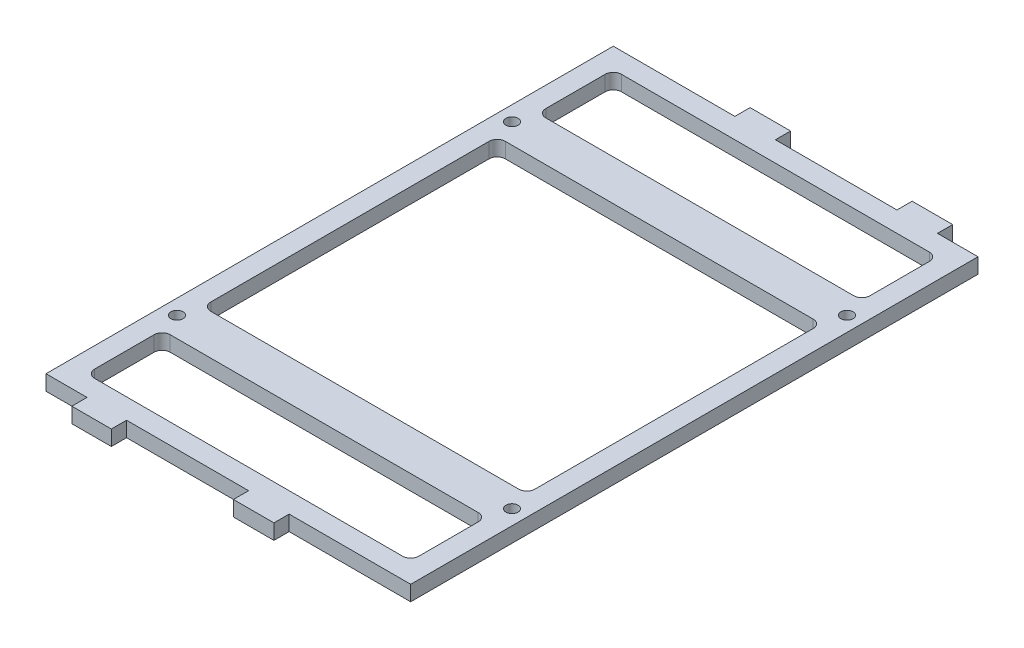
SolidWorks part; units mm, degrees
material "6061-T6 (SS)"
ref_plane "Front Plane" through (0, 0, 0) normal (0, 0, 1) x (1, 0, 0)
ref_plane "Top Plane" through (0, 0, 0) normal (0, 1, 0) x (1, 0, 0)
ref_plane "Right Plane" through (0, 0, 0) normal (1, 0, 0) x (0, 0, -1)
sketch "Sketch1" plane through (0, 0, 0) normal (0, 1, 0) x (1, 0, 0)
  line L0 (50.8, 82.55) -> (-50.8, 82.55)
  line L1 (57.15, 88.9) -> (-57.15, 88.9)
  line L2 (57.15, 88.9) -> (57.15, -88.9)
  line L3 (57.15, -88.9) -> (-57.15, -88.9)
  line L4 (-57.15, 88.9) -> (-57.15, -88.9)
  line L5 (57.15, 88.9) -> (-57.15, -88.9) construction
  line L6 (57.15, -88.9) -> (-57.15, 88.9) construction
  line L7 (-50.8, 82.55) -> (-50.8, -82.55)
  line L8 (50.8, -82.55) -> (-50.8, -82.55)
  line L9 (50.8, 82.55) -> (50.8, -82.55)
  point P0 (0, 0)
  dimension "D1" = 114.3
  dimension "D2" = 177.8
  dimension "D3" = 6.35
extrude "Boss-Extrude1" add sketch "Sketch1" along normal blind 4.7625
sketch "Sketch2" plane through (0, 0, 88.9) normal (0, 0, 1) x (1, 0, 0)
  line L0 (-57.15, 2.3813) -> (57.15, 2.3813) construction
  line L1 (-57.15, 4.7625) -> (-57.15, 0) construction
  line L2 (57.15, 4.7625) -> (57.15, 0) construction
  line L3 (-57.15, 0) -> (57.15, 0) construction
  line L4 (-31.9066, 4.7625) -> (-44.2934, 4.7625)
  line L5 (-31.9066, 4.7625) -> (-31.9066, 0)
  line L6 (-31.9066, 0) -> (-44.2934, 0)
  line L7 (-44.2934, 4.7625) -> (-44.2934, 0)
  line L8 (-31.9066, 4.7625) -> (-44.2934, 0) construction
  line L9 (-31.9066, 0) -> (-44.2934, 4.7625) construction
  line L11 (19.05, 4.7625) -> (6.35, 4.7625)
  line L12 (19.05, 4.7625) -> (19.05, 0)
  line L13 (19.05, 0) -> (6.35, 0)
  line L14 (6.35, 4.7625) -> (6.35, 0)
  line L15 (19.05, 4.7625) -> (6.35, 0) construction
  line L16 (19.05, 0) -> (6.35, 4.7625) construction
  point P6 (-38.1, 2.3813)
  point P13 (12.7, 2.3813)
  dimension "D1" = 19.05
  dimension "D2" = 50.8
  dimension "D3" = 12.7
extrude "Boss-Extrude2" add sketch "Sketch2" along normal blind 4.7625
sketch "Sketch3" plane through (0, 0, -88.9) normal (0, 0, -1) x (-1, 0, 0)
  line L0 (-57.15, 2.3813) -> (57.15, 2.3813) construction
  line L1 (-57.15, 4.7625) -> (-57.15, 0) construction
  line L2 (57.15, 4.7625) -> (57.15, 0) construction
  line L3 (-57.15, 0) -> (57.15, 0) construction
  line L4 (-31.75, 4.7625) -> (-44.45, 4.7625)
  line L5 (-31.75, 4.7625) -> (-31.75, 0)
  line L6 (-31.75, 0) -> (-44.45, 0)
  line L7 (-44.45, 4.7625) -> (-44.45, 0)
  line L8 (-31.75, 4.7625) -> (-44.45, 0) construction
  line L9 (-31.75, 0) -> (-44.45, 4.7625) construction
  line L11 (19.05, 4.7625) -> (6.35, 4.7625)
  line L12 (19.05, 4.7625) -> (19.05, 0)
  line L13 (19.05, 0) -> (6.35, 0)
  line L14 (6.35, 4.7625) -> (6.35, 0)
  line L15 (19.05, 4.7625) -> (6.35, 0) construction
  line L16 (19.05, 0) -> (6.35, 4.7625) construction
  point P6 (-38.1, 2.3812)
  point P13 (12.7, 2.3812)
  dimension "D1" = 12.7
  dimension "D2" = 12.7
  dimension "D3" = 19.05
  dimension "D4" = 50.8
extrude "Boss-Extrude3" add sketch "Sketch3" along normal blind 4.7625
fillet "Fillet1" radius 2.54 4 edges at (50.8, 2.3813, 82.55) (50.8, 2.3813, -82.55) (-50.8, 2.3813, -82.55) (-50.8, 2.3813, 82.55)
sketch "Sketch4" plane through (0, 4.7625, 0) normal (0, 1, 0) x (1, 0, 0)
  line L0 (0, 82.55) -> (0, -82.55) construction
  line L1 (48.26, 82.55) -> (-48.26, 82.55) construction
  line L2 (-48.26, -82.55) -> (48.26, -82.55) construction
  line L3 (-57.15, 88.9) -> (-57.15, -88.9) construction
  line L4 (57.15, 58.85) -> (-57.15, 58.85)
  line L5 (57.15, 58.85) -> (57.15, 46.15)
  line L6 (57.15, 46.15) -> (-57.15, 46.15)
  line L7 (-57.15, 58.85) -> (-57.15, 46.15)
  line L8 (57.15, 58.85) -> (-57.15, 46.15) construction
  line L9 (57.15, 46.15) -> (-57.15, 58.85) construction
  line L11 (57.15, -46.15) -> (-57.15, -46.15)
  line L12 (57.15, -46.15) -> (57.15, -58.85)
  line L13 (57.15, -58.85) -> (-57.15, -58.85)
  line L14 (-57.15, -46.15) -> (-57.15, -58.85)
  line L15 (57.15, -46.15) -> (-57.15, -58.85) construction
  line L16 (57.15, -58.85) -> (-57.15, -46.15) construction
  point P6 (0, 52.5)
  point P13 (0, -52.5)
  dimension "D1" = 12.7
  dimension "D2" = 12.7
  dimension "D3" = 52.5
  dimension "D4" = 52.5
extrude "Boss-Extrude4" add sketch "Sketch4" against normal blind 4.7625
hole_wizard "#6 Clearance Hole1" positions "Sketch6" profile "Sketch5" hole size "#6" standard "Ansi Inch"
sketch "Sketch6" plane through (0, 4.7625, 0) normal (0, 1, 0) x (-1, 0, 0)
  line L0 (50.8, -58.85) -> (50.8, -46.15) construction
  line L2 (50.8, -52.5) -> (-57.15, -52.5) construction
  line L3 (-57.15, 88.9) -> (-57.15, -88.9) construction
  line L5 (50.8, 58.85) -> (50.8, 46.15) construction
  line L7 (0, 58.85) -> (0, 46.15) construction
  line L8 (50.8, 58.85) -> (-50.8, 58.85) construction
  line L9 (-50.8, 46.15) -> (50.8, 46.15) construction
  line L11 (50.8, 52.5) -> (-57.15, 52.5) construction
  point P0 (52.5, -52.5)
  point P1 (-52.5, -52.5)
  point P3 (52.5, 52.5)
  point P5 (-52.5, 52.5)
  dimension "D1" = 52.5
  dimension "D2" = 52.5
  dimension "D3" = 52.5
  dimension "D4" = 52.5
sketch "Sketch5" plane through (-52.5, 4.7625, -52.5) normal (1, 0, 0) x (0, 0, 1)
  line L0 (0, 0) -> (0, 26.5408)
  line L1 (0, 26.5408) -> (1.8986, 25.4)
  line L2 (1.8986, 25.4) -> (1.8986, 0)
  line L5 (1.8986, 0) -> (0, 0)
  line L10 (0, 26.5408) -> (-1.8987, 25.4) construction
  line L11 (0, -6.35) -> (0, 107.95) construction
  dimension "Hole Dia." = 3.7973
  dimension "Hole Depth" = 25.4
  dimension "Drill Angle" = 118
fillet "Fillet2" radius 2.54 8 edges at (-50.8, 2.3813, -58.85) (-50.8, 2.3813, -46.15) (50.8, 2.3813, -58.85) (50.8, 2.3813, -46.15) (50.8, 2.3813, 46.15) (-50.8, 2.3813, 46.15) (-50.8, 2.3813, 58.85) (50.8, 2.3813, 58.85)
